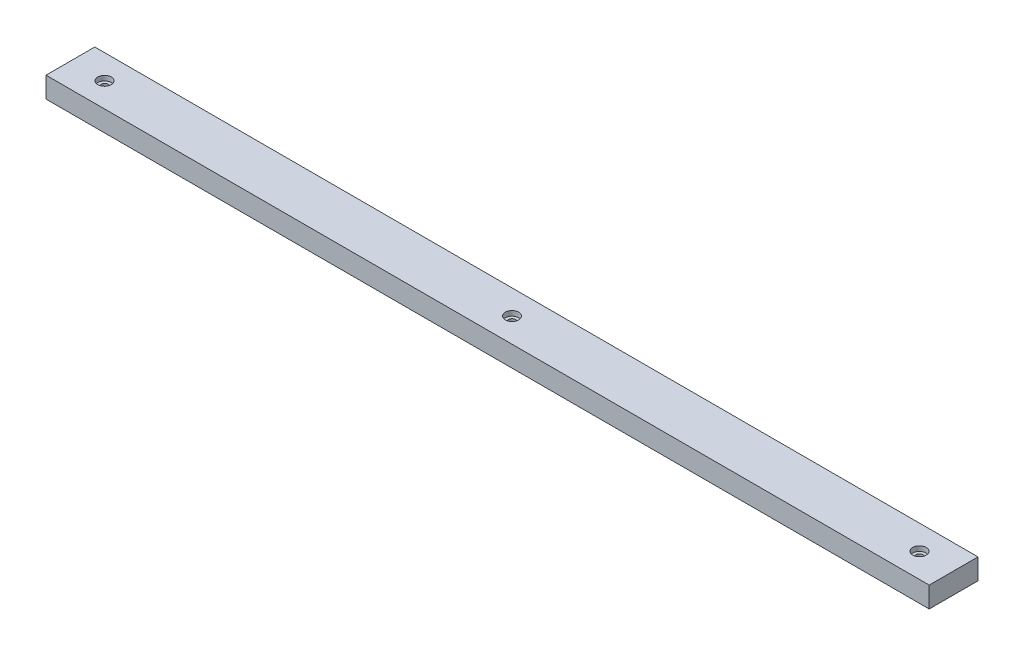
SolidWorks part; units mm, degrees
material "Chêne"
ref_plane "Plan de face" through (0, 0, 0) normal (0, 0, 1) x (1, 0, 0)
ref_plane "Plan de dessus" through (0, 0, 0) normal (0, 1, 0) x (1, 0, 0)
ref_plane "Plan de droite" through (0, 0, 0) normal (1, 0, 0) x (0, 0, -1)
sketch "Esquisse1" plane through (0, 0, 0) normal (0, 0, 1) x (1, 0, 0)
  line L4 (181, 0) -> (-181, 0)
  line L5 (-181, 0) -> (-181, -8.5)
  line L6 (-181, -8.5) -> (181, -8.5)
  line L7 (181, -8.5) -> (181, 0)
  line L8 (181, 0) -> (-181, 0)
  line L9 (-181, 0) -> (-181, -8.5)
  line L10 (-181, -8.5) -> (181, -8.5)
  line L11 (181, -8.5) -> (181, 0)
  dimension "D1" = 0
extrude "Boss.-Extru.1" add sketch "Esquisse1" along normal blind 20 contours L10 L11 L8 L9
hole_wizard "Chambrage pour vis à tête cylindrique courte six pans creux M31" positions "Esquisse2" profile "Esquisse3" counterbore size "M3" standard "DIN" end condition through all
sketch "Esquisse2" plane through (0, 0, 0) normal (0, 1, 0) x (1, 0, 0)
  line L0 (-181, -20) -> (-181, 0) construction
  line L1 (-181, -20) -> (-181, 0) construction
  line L2 (181, -20) -> (181, 0) construction
  point P0 (-167, -10)
  point P3 (167, -10)
  point P7 (0, -10)
  point P23 (-181, -10)
  dimension "D1" = 14
  dimension "D2" = 14
  dimension "D3" = 167
sketch "Esquisse3" plane through (-167, 0, 10) normal (1, 0, 0) x (0, 0, 1)
  line L0 (0, 0) -> (0, 8.5)
  line L1 (0, 8.5) -> (1.5, 8.5)
  line L3 (1.5, 8.5) -> (1.5, 2)
  line L4 (1.5, 2) -> (2.75, 2)
  line L5 (2.75, 2) -> (2.75, 0)
  line L7 (2.75, 0) -> (0, 0)
  line L11 (0, -6.35) -> (0, 107.95) construction
  dimension "Diamètre du perçage jusqu'au prochain" = 3
  dimension "Profondeur du perçage jusqu'au prochain" = 8.5
  dimension "Diamètre du chambrage" = 5.5
  dimension "Profondeur du chambrage" = 2
